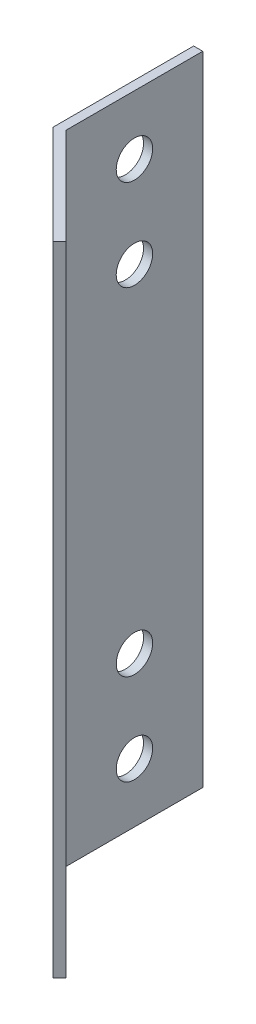
SolidWorks part; units mm, degrees
ref_plane "Face" through (0, 0, 0) normal (0, 0, 1) x (1, 0, 0)
ref_plane "Dessus" through (0, 0, 0) normal (0, 1, 0) x (1, 0, 0)
ref_plane "Droite" through (0, 0, 0) normal (1, 0, 0) x (0, 0, -1)
sketch "Esquisse1" plane through (0, 0, 0) normal (0, 1, 0) x (1, 0, 0)
  line L0 (0, 0) -> (0, 15.4142)
  line L1 (0, 15.4142) -> (1, 15.4142)
  line L2 (1, 15.4142) -> (1, 0.4142)
  line L3 (1, 0.4142) -> (11.6066, -10.1924)
  line L4 (11.6066, -10.1924) -> (10.8995, -10.8995)
  line L5 (10.8995, -10.8995) -> (0, 0)
  dimension "D1" = 1
  dimension "D2" = 1
  dimension "D3" = 45
  dimension "D4" = 15
extrude "Extrusion1" add sketch "Esquisse1" along normal blind 70
sketch "Esquisse2" plane through (1, 0, 0) normal (1, 0, 0) x (0, 0, -1)
  line L0 (0.4142, 35) -> (15.4142, 35) construction
  line L1 (0.4142, 70) -> (0.4142, 0) construction
  line L2 (15.4142, 70) -> (15.4142, 0) construction
  line L3 (7.9142, 0) -> (7.9142, 70) construction
  line L4 (0.4142, 0) -> (15.4142, 0) construction
  line L5 (0.4142, 70) -> (15.4142, 70) construction
  circle A0 centre (7.9142, 16.5) radius 2
  circle A1 centre (7.9142, 6.5) radius 2
  circle A2 centre (7.9142, 53.5) radius 2
  circle A3 centre (7.9142, 63.5) radius 2
  dimension "D1" = 4
  dimension "D2" = 18.5
  dimension "D3" = 10
extrude "Extrusion2" cut sketch "Esquisse2" against normal up to next
sketch "Esquisse3" plane through (0.7071, 0, -0.7071) normal (0.7071, 0, -0.7071) x (-0.7071, 0, -0.7071)
  line L0 (-7.9142, 70) -> (-7.9142, 0) construction
  line L1 (-15.4142, 70) -> (-0.4142, 70) construction
  line L2 (-15.4142, 0) -> (-0.4142, 0) construction
  line L3 (-15.4142, 35) -> (-0.4142, 35) construction
  line L4 (-15.4142, 70) -> (-15.4142, 0) construction
  line L5 (-0.4142, 70) -> (-0.4142, 0) construction
  circle A0 centre (-7.9142, 53.5) radius 2
  circle A1 centre (-7.9142, 63.5) radius 2
  circle A2 centre (-7.9142, 6.5) radius 2
  circle A3 centre (-7.9142, 16.5) radius 2
  dimension "D1" = 4
  dimension "D2" = 18.5
  dimension "D3" = 10
extrude "Extrusion3" cut sketch "Esquisse3" against normal up to next
